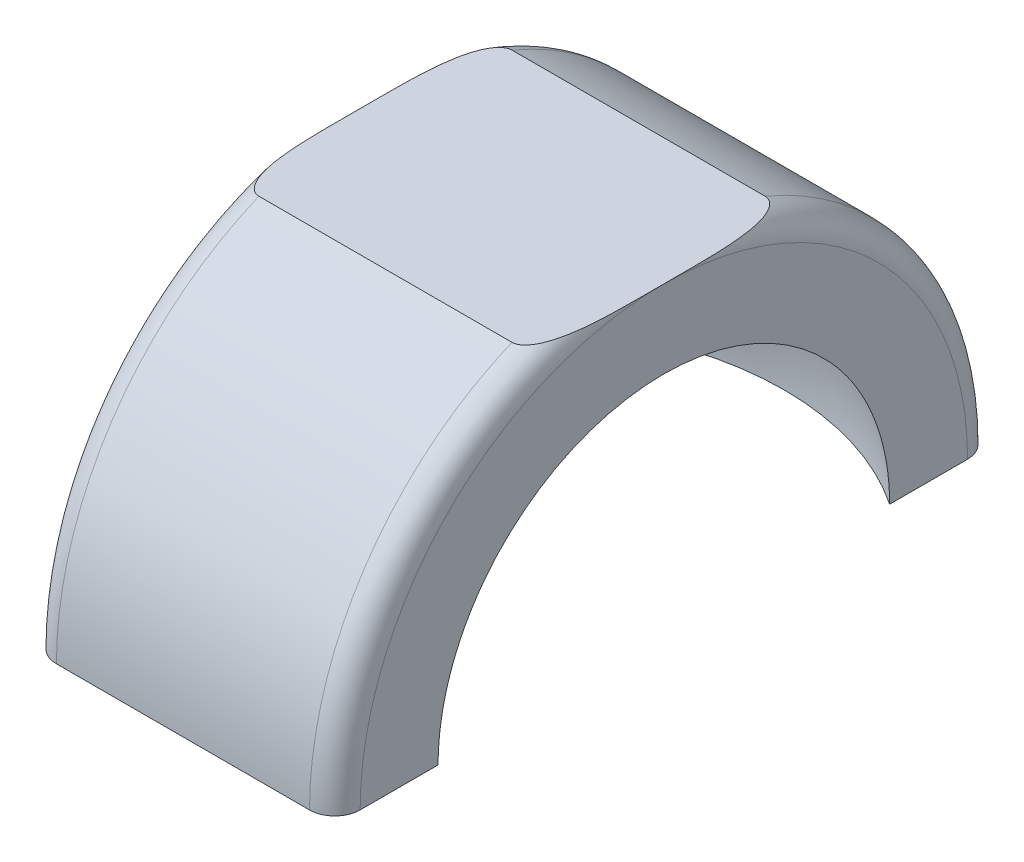
SolidWorks part; units mm, degrees
ref_plane "Plan1" through (0, 0, 0) normal (0, 0, 1) x (1, 0, 0)
ref_plane "Plan2" through (0, 0, 0) normal (0, 1, 0) x (1, 0, 0)
ref_plane "Plan3" through (0, 0, 0) normal (1, 0, 0) x (0, 0, -1)
sketch "Esquisse1" plane through (0, 0, 0) normal (0, 0, 1) x (1, 0, 0)
  line L0 (-22, 0) -> (23, 0) construction
  line L2 (-12, 17.8396) -> (-12, 24)
  line L3 (12, 17.8396) -> (12, 24)
  line L4 (-10, 26) -> (10, 26)
  arc A0 (12, 17.8396) -> (-12, 17.8396) centre (0, 0) ccw
  arc A1 (-10, 26) -> (-12, 24) centre (-10, 24) ccw
  arc A2 (12, 24) -> (10, 26) centre (10, 24) ccw
  point P9 (-12, 26)
  point P12 (0, 26)
  point P14 (12, 26)
  dimension "D1" = 43
  dimension "D4" = 2
  dimension "D2" = 24
  dimension "D3" = 26
revolve "Base-Révolution" add sketch "Esquisse1" angle 180 mid plane about L0
sketch "Esquisse2" plane through (12, 0, 0) normal (1, 0, 0) x (0, 0, -1)
  line L0 (-22, 24) -> (22, 24)
  line L1 (22, 24) -> (22, 30)
  line L2 (22, 30) -> (-22, 30)
  line L3 (-22, 30) -> (-22, 24)
  dimension "D1" = 24
extrude "Enlèv. mat.-Extru.1" cut sketch "Esquisse2" against normal through all
